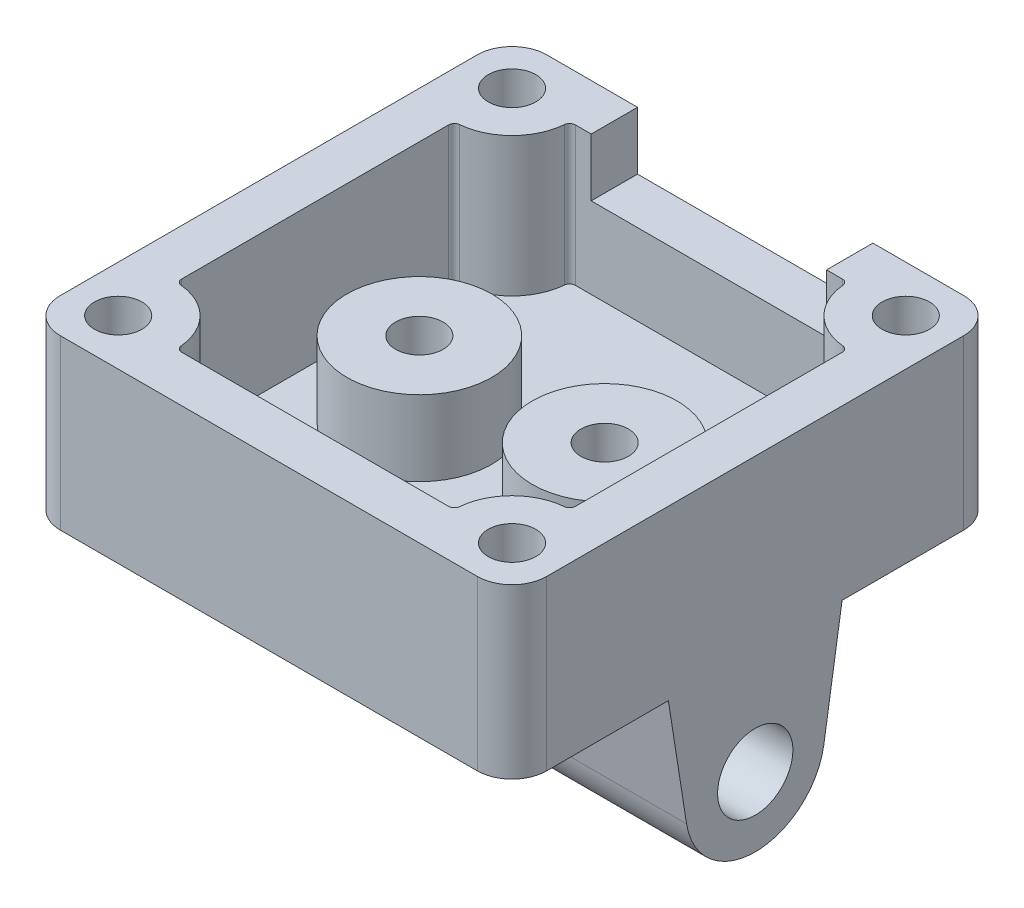
SolidWorks part; units mm, degrees
material "ABS"
ref_plane "Front Plane" through (0, 0, 0) normal (0, 0, 1) x (1, 0, 0)
ref_plane "Top Plane" through (0, 0, 0) normal (0, 1, 0) x (1, 0, 0)
ref_plane "Right Plane" through (0, 0, 0) normal (1, 0, 0) x (0, 0, -1)
sketch "Sketch1" plane through (0, 0, 0) normal (0, 1, 0) x (1, 0, 0)
  line L1 (-21, 21) -> (21, 21)
  line L2 (-21, 21) -> (-21, -21)
  line L3 (-21, -21) -> (21, -21)
  line L4 (21, 21) -> (21, -21)
  line L5 (-21, 21) -> (21, -21) construction
  line L6 (-21, -21) -> (21, 21) construction
  point P0 (0, 0)
  dimension "D1" = 42
  dimension "D2" = 42
extrude "Boss-Extrude1" add sketch "Sketch1" along normal blind 2.54
sketch "Sketch2" plane through (0, 2.54, 0) normal (0, 1, 0) x (1, 0, 0)
  line L26 (-21, 21) -> (21, 21)
  line L44 (-21, 21) -> (-21, -21)
  line L45 (-21, -21) -> (21, -21)
  line L49 (21, 21) -> (21, -21)
  line L50 (-21, 21) -> (21, -21) construction
  line L51 (-21, -21) -> (21, 21) construction
  line L55 (-17, 11.5228) -> (-17, -11.5228)
  line L56 (-11.5228, -17) -> (11.5228, -17)
  line L57 (17, 11.5228) -> (17, -11.5228)
  line L58 (-11.5228, 17) -> (11.5228, 17)
  line L63 (-17, 17) -> (-17, -17) construction
  line L64 (-17, -17) -> (17, -17) construction
  line L65 (17, 17) -> (17, -17) construction
  line L66 (-17, 17) -> (17, 17) construction
  line L68 (-13.4645, 13.4645) -> (13.4645, 13.4645) construction
  line L69 (-13.4645, 13.4645) -> (-13.4645, -13.4645) construction
  line L70 (-13.4645, -13.4645) -> (13.4645, -13.4645) construction
  line L71 (13.4645, 13.4645) -> (13.4645, -13.4645) construction
  line L72 (-13.4645, 13.4645) -> (13.4645, -13.4645) construction
  line L73 (-13.4645, -13.4645) -> (13.4645, 13.4645) construction
  arc A0 (-16.5455, -12.0207) -> (-12.0207, -16.5455) centre (-17, -17) cw
  arc A2 (12.0207, -16.5455) -> (16.5455, -12.0207) centre (17, -17) cw
  arc A4 (16.5455, 12.0207) -> (12.0207, 16.5455) centre (17, 17) cw
  arc A6 (-12.0207, 16.5455) -> (-16.5455, 12.0207) centre (-17, 17) cw
  arc A8 (-16.5455, -12.0207) -> (-17, -11.5228) centre (-16.5, -11.5228) cw
  arc A9 (-12.0207, -16.5455) -> (-11.5228, -17) centre (-11.5228, -16.5) ccw
  arc A10 (12.0207, -16.5455) -> (11.5228, -17) centre (11.5228, -16.5) cw
  arc A11 (16.5455, -12.0207) -> (17, -11.5228) centre (16.5, -11.5228) ccw
  arc A12 (16.5455, 12.0207) -> (17, 11.5228) centre (16.5, 11.5228) cw
  arc A13 (12.0207, 16.5455) -> (11.5228, 17) centre (11.5228, 16.5) ccw
  arc A14 (-12.0207, 16.5455) -> (-11.5228, 17) centre (-11.5228, 16.5) cw
  arc A15 (-16.5455, 12.0207) -> (-17, 11.5228) centre (-16.5, 11.5228) ccw
  point P0 (0, 0)
  point P44 (0, 0)
  dimension "D2" = 5
  dimension "D3" = 0.5
  dimension "D1" = 4
  dimension "D4" = 26.9289
  dimension "D5" = 26.9289
extrude "Boss-Extrude2" add sketch "Sketch2" along normal blind 12
sketch "Sketch4" plane through (-21, 0, 0) normal (-1, 0, 0) x (0, 0, 1)
  line L0 (7.5, 0) -> (5.9271, -10)
  line L1 (-21, 0) -> (21, 0) construction
  line L2 (-5.9271, -10) -> (-7.5, 0)
  line L3 (7.5, 0) -> (-7.5, 0)
  arc A0 (5.9271, -10) -> (-5.9271, -10) centre (0, -9.0677) cw
  circle A1 centre (0, -9.0677) radius 3.25
  point P6 (5.989, 0)
  point P10 (2.9491, 0)
  point P11 (0, 0)
  point P12 (0, 0)
  dimension "D1" = 6.5
  dimension "D4" = 6
  dimension "D2" = 10
  dimension "D3" = 15
extrude "Boss-Extrude4" add sketch "Sketch4" against normal up to surface (42 mm away) up to face at (21, 7.27, 0)
mirror "Mirror1" [suppressed] about plane through (0, 0, 0) normal (1, 0, 0)
sketch "Sketch9" plane through (0, 2.54, 0) normal (0, 1, 0) x (1, 0, 0)
  line L0 (0, -1.397) -> (0, 1.397) construction
  line L1 (0, 0) -> (-8, 0) construction
  circle A0 centre (8, 0) radius 2.05
  circle A1 centre (8, 0) radius 6.25
  circle A2 centre (-8, 0) radius 6.25
  circle A3 centre (-8, 0) radius 2.05
  dimension "D1" = 4.1
  dimension "D2" = 4.2
  dimension "D3" = 8
extrude "Boss-Extrude5" add sketch "Sketch9" along normal blind 6.5
sketch "Sketch10" plane through (0, 14.54, 0) normal (0, 1, 0) x (1, 0, 0)
  circle A0 centre (-17, 17) radius 2.05
  circle A1 centre (17, 17) radius 2.05
  circle A2 centre (-17, -17) radius 2.05
  circle A3 centre (17, -17) radius 2.05
  dimension "D1" = 4.1
extrude "Cut-Extrude1" cut sketch "Sketch10" against normal blind 8
sketch "Sketch12" plane through (0, 0, -21) normal (0, 0, -1) x (-1, 0, 0)
  line L0 (-21, 14.54) -> (21, 14.54) construction
  line L1 (10.16, 9.54) -> (-10.16, 9.54)
  line L2 (10.16, 9.54) -> (10.16, 14.54)
  line L3 (10.16, 14.54) -> (-10.16, 14.54)
  line L4 (-10.16, 9.54) -> (-10.16, 14.54)
  line L5 (10.16, 9.54) -> (-10.16, 14.54) construction
  line L6 (10.16, 14.54) -> (-10.16, 9.54) construction
  point P0 (0, 12.04)
  point P7 (0, 14.54)
  point P8 (0, 14.54)
  dimension "D1" = 5
  dimension "D2" = 20.32
extrude "Cut-Extrude2" cut sketch "Sketch12" against normal up to surface (4 mm away) up to face at (0, 8.54, -17)
fillet "Fillet1" radius 3 4 edges at (21, 7.27, 21) (-21, 7.27, 21) (-21, 7.27, -21) (21, 7.27, -21)
